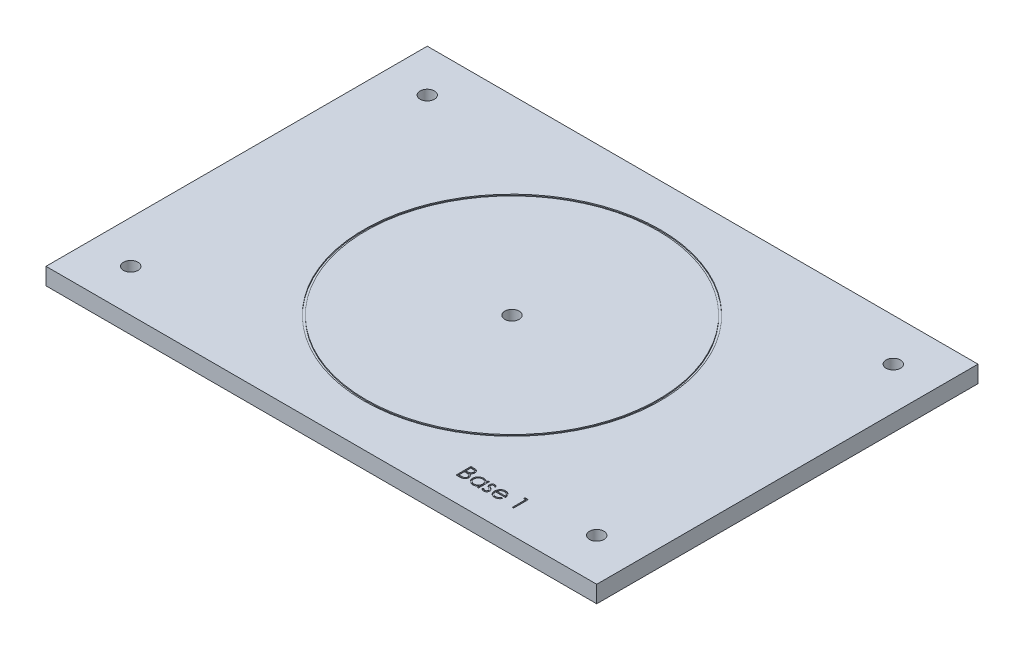
SolidWorks part; units mm, degrees
material "Acrílico (Impacto medio-alto)"
ref_plane "Alzado" through (0, 0, 0) normal (0, 0, 1) x (1, 0, 0)
ref_plane "Planta" through (0, 0, 0) normal (0, 1, 0) x (1, 0, 0)
ref_plane "Vista lateral" through (0, 0, 0) normal (1, 0, 0) x (0, 0, -1)
sketch "Croquis1" plane through (0, 0, 0) normal (0, 1, 0) x (1, 0, 0)
  line L1 (65, -45) -> (-65, -45)
  line L2 (65, -45) -> (65, 45)
  line L3 (65, 45) -> (-65, 45)
  line L4 (-65, -45) -> (-65, 45)
  line L5 (65, -45) -> (-65, 45) construction
  line L6 (65, 45) -> (-65, -45) construction
  point P0 (0, 0)
  dimension "D1" = 90
  dimension "D2" = 130
extrude "Saliente-Extruir1" add sketch "Croquis1" along normal mid plane 4
hole_wizard "Taladro de margen para M31" positions "Croquis3" profile "Croquis2" hole size "M3" standard "Din"
sketch "Croquis3" plane through (0, 2, 0) normal (0, 1, 0) x (1, 0, 0)
  line L0 (65, 45) -> (-65, 45) construction
  line L1 (-65, 45) -> (-65, -45) construction
  line L2 (65, -45) -> (65, 45) construction
  line L3 (-65, -45) -> (65, -45) construction
  point P0 (-55, 35)
  point P2 (55, 35)
  point P4 (55, -35)
  point P6 (-55, -35)
  dimension "D1" = 10
  dimension "D2" = 10
  dimension "D3" = 10
  dimension "D4" = 10
  dimension "D5" = 10
  dimension "D6" = 10
  dimension "D7" = 10
  dimension "D8" = 10
sketch "Croquis2" plane through (-55, 2, -35) normal (1, 0, 0) x (0, 0, 1)
  line L0 (0, 0) -> (0, 41.0215)
  line L1 (0, 41.0215) -> (1.7, 40)
  line L2 (1.7, 40) -> (1.7, 0)
  line L5 (1.7, 0) -> (0, 0)
  line L10 (0, 41.0215) -> (-1.7, 40) construction
  line L11 (0, -6.35) -> (0, 107.95) construction
  dimension "Diámetro de taladro" = 3.4
  dimension "Profundidad de taladro" = 40
  dimension "Ángulo de perforador" = 118
sketch "Croquis4" plane through (0, 2, 0) normal (0, 1, 0) x (1, 0, 0)
  line L0 (15.1417, -39.2641) -> (51.273, -39.2641) construction
  text T0 "Base 1"
extrude "Cortar-Extruir1" cut sketch "Croquis4" against normal blind 0.25
sketch "Croquis5" plane through (0, 2, 0) normal (0, 1, 0) x (1, 0, 0)
  line L1 (65, 45) -> (-65, 45) construction
  circle A0 centre (0, 0) radius 34.5
  circle A1 centre (0, 0) radius 35
  dimension "D1" = 10
  dimension "D2" = 0.5
extrude "Cortar-Extruir2" cut sketch "Croquis5" against normal blind 0.25
hole_wizard "Taladro de margen para M32" positions "Croquis7" profile "Croquis6" hole size "M3" standard "DIN" end condition through all
sketch "Croquis7" plane through (0, 2, 0) normal (0, 1, 0) x (1, 0, 0)
  point P0 (0, 0)
sketch "Croquis6" plane through (0, 2, 0) normal (1, 0, 0) x (0, 0, 1)
  line L0 (0, 0) -> (0, 4)
  line L1 (0, 4) -> (1.7, 4)
  line L2 (1.7, 4) -> (1.7, 0)
  line L5 (1.7, 0) -> (0, 0)
  line L11 (0, -6.35) -> (0, 107.95) construction
  dimension "Diámetro de taladro hasta el siguiente" = 3.4
  dimension "Profundidad de taladro hasta el siguiente" = 4
equation "\"Grosor de Acrilico\"= 4mm"
